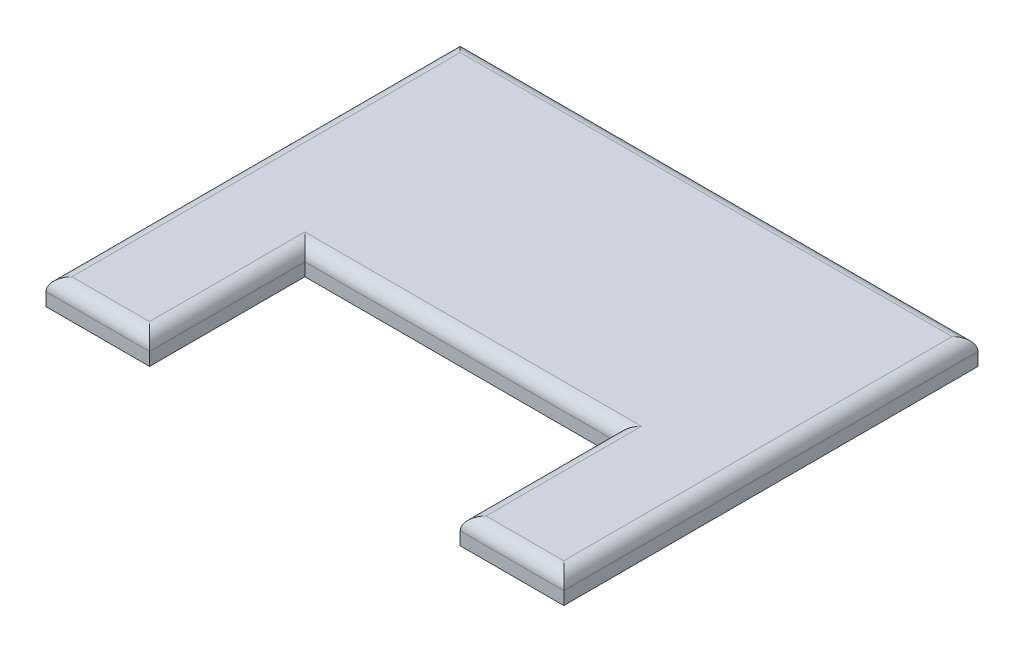
SolidWorks part; units mm, degrees
material "PUR"
ref_plane "Front Plane" through (0, 0, 0) normal (0, 0, 1) x (1, 0, 0)
ref_plane "Top Plane" through (0, 0, 0) normal (0, 1, 0) x (1, 0, 0)
ref_plane "Right Plane" through (0, 0, 0) normal (1, 0, 0) x (0, 0, -1)
sketch "Sketch1" plane through (0, 0, 0) normal (0, 1, 0) x (1, 0, 0)
  line L0 (-60, -80) -> (-60, -20)
  line L1 (-100, 80) -> (100, 80)
  line L2 (-100, 80) -> (-100, -80)
  line L3 (-100, -80) -> (-60, -80)
  line L4 (100, 80) -> (100, -80)
  line L5 (-100, 80) -> (100, -80) construction
  line L6 (-100, -80) -> (100, 80) construction
  line L7 (-60, -20) -> (60, -20)
  line L8 (60, -20) -> (60, -80)
  line L9 (60, -80) -> (100, -80)
  point P0 (0, 0)
  dimension "D1" = 160
  dimension "D2" = 200
  dimension "D3" = 60
  dimension "D4" = 120
  dimension "D5" = 40
extrude "Boss-Extrude1" add sketch "Sketch1" along normal blind 10
fillet "Fillet1" radius 5 8 edges at (60, 10, 50) (0, 10, 20) (-60, 10, 50) (-80, 10, 80) (-100, 10, 0) (0, 10, -80) (100, 10, 0) (80, 10, 80)
